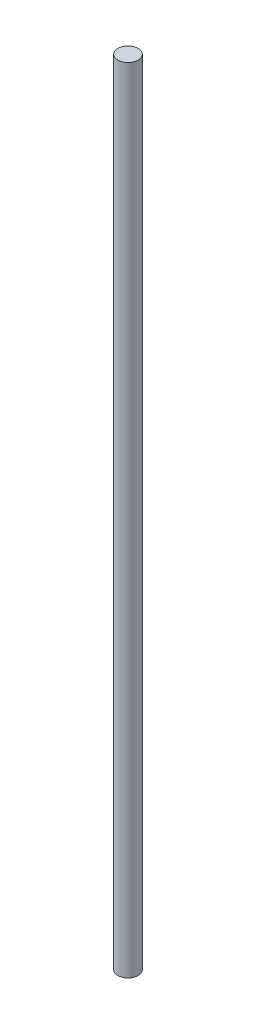
SolidWorks part; units mm, degrees
material "AISI 304"
ref_plane "Front Plane" through (0, 0, 0) normal (0, 0, 1) x (1, 0, 0)
ref_plane "Top Plane" through (0, 0, 0) normal (0, 1, 0) x (1, 0, 0)
ref_plane "Right Plane" through (0, 0, 0) normal (1, 0, 0) x (0, 0, -1)
sketch "Sketch1" plane through (0, 0, 0) normal (0, 1, 0) x (1, 0, 0)
  circle A0 centre (0, 0) radius 3
  dimension "D1" = 6
extrude "Boss-Extrude1" add sketch "Sketch1" along normal blind 235
